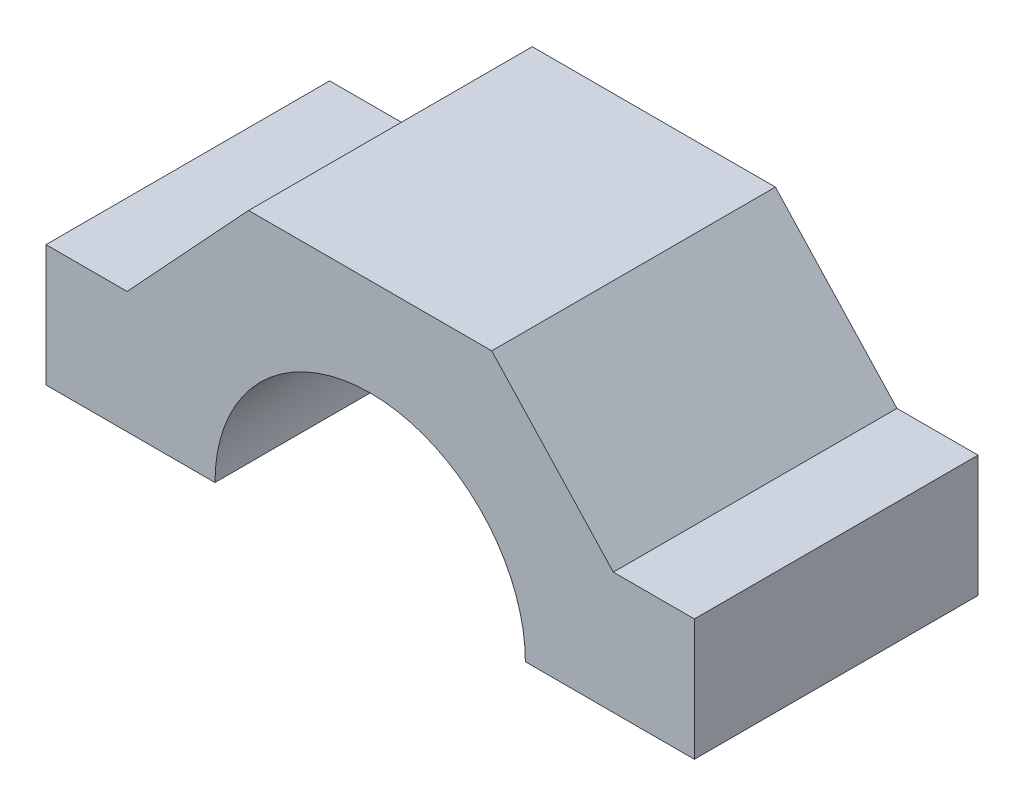
SolidWorks part; units mm, degrees
ref_plane "Front Plane" through (0, 0, 0) normal (0, 0, 1) x (1, 0, 0)
ref_plane "Top Plane" through (0, 0, 0) normal (0, 1, 0) x (1, 0, 0)
ref_plane "Right Plane" through (0, 0, 0) normal (1, 0, 0) x (0, 0, -1)
sketch "Sketch1" plane through (0, 0, 0) normal (0, 0, 1) x (1, 0, 0)
  line L0 (19.15, 0) -> (40, 0)
  line L6 (-40, 0) -> (-40, 15)
  line L7 (-40, 15) -> (-30, 15)
  line L8 (-30, 15) -> (-15, 31.15)
  line L9 (-15, 31.15) -> (15, 31.15)
  line L18 (0, 31.15) -> (0, 0) construction
  line L19 (-40, 0) -> (-19.15, 0)
  line L20 (30, 15) -> (15, 31.15)
  line L21 (40, 15) -> (30, 15)
  line L22 (40, 0) -> (40, 15)
  arc A1 (-19.15, 0) -> (19.15, 0) centre (0, 0) cw
  point P0 (0, 0)
  point P27 (0, 19.15)
  point P28 (55.8231, -4.2139)
  dimension "D2" = 19.15
  dimension "D4" = 12
  dimension "D1" = 15
  dimension "D5" = 80
  dimension "D6" = 10
  dimension "D7" = 30
extrude "Boss-Extrude3" add sketch "Sketch1" along normal blind 35
sketch "Sketch6" plane through (0, 0, 0) normal (0, 0, -1) x (-1, 0, 0)
  line L0 (-19.15, 0) -> (-7.5, 0)
  line L1 (7.5, 0) -> (19.15, 0)
  arc A0 (-7.5, 0) -> (7.5, 0) centre (0, 0) cw
  arc A3 (19.15, 0) -> (-19.15, 0) centre (0, 0) ccw
  arc A4 (19.15, 0) -> (-19.15, 0) centre (0, 0) ccw
  dimension "D2" = 7.5
  dimension "D1" = 0
extrude "Boss-Extrude4" add sketch "Sketch6" against normal blind 3
sketch "Sketch4" plane through (0, 0, 3) normal (0, 0, 1) x (1, 0, 0)
  line L0 (0, 0) -> (0, 19.15) construction
  line L1 (0, 0) -> (9.1924, 9.1924) construction
  arc A3 (19.15, 0) -> (-19.15, 0) centre (0, 0) ccw construction
  circle A5 centre (9.1924, 9.1924) radius 1.5
  circle A6 centre (-9.1924, 9.1924) radius 1.5
  dimension "D2" = 3
  dimension "D1" = 13
  dimension "D3" = 45
extrude "Cut-Extrude2" cut sketch "Sketch4" against normal through all
